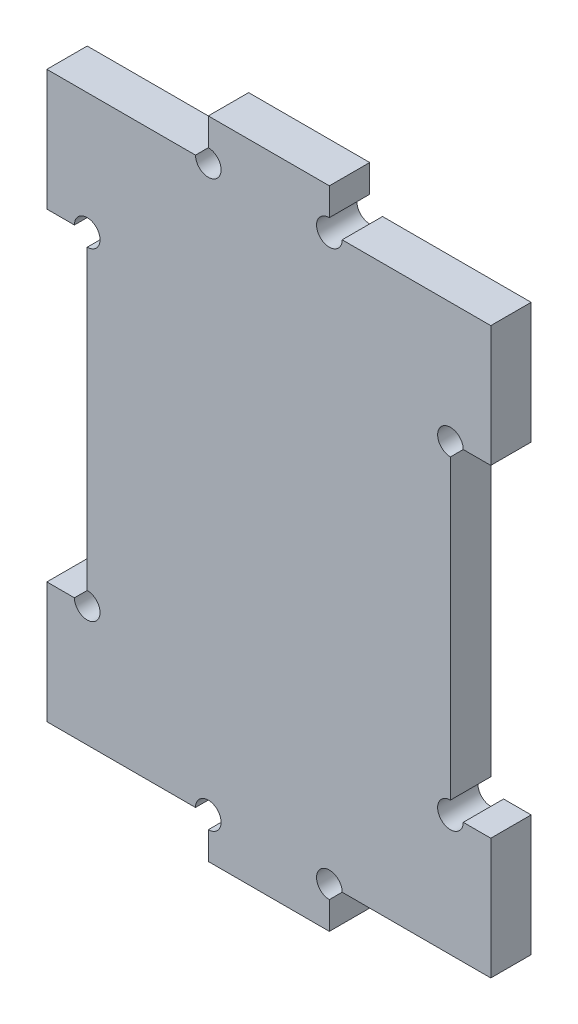
SolidWorks part; units mm, degrees
material "Acrylic (Medium-high impact)"
ref_plane "Front Plane" through (0, 0, 0) normal (0, 0, 1) x (1, 0, 0)
ref_plane "Top Plane" through (0, 0, 0) normal (0, 1, 0) x (1, 0, 0)
ref_plane "Right Plane" through (0, 0, 0) normal (1, 0, 0) x (0, 0, -1)
sketch "Sketch2" plane through (0, 0, 0) normal (0, 0, 1) x (1, 0, 0)
  line L0 (-7.5, 40) -> (7.5, 40)
  line L1 (7.5, 40) -> (7.5, 35)
  line L2 (7.5, 35) -> (27.5, 35)
  line L3 (27.5, 35) -> (27.5, -35)
  line L4 (0, 0) -> (27.5, 0) construction
  line L5 (0, -40) -> (0, 40) construction
  line L6 (-27.5, 35) -> (-27.5, -35)
  line L7 (-7.5, 35) -> (-27.5, 35)
  line L8 (-7.5, 40) -> (-7.5, 35)
  line L9 (-7.5, -40) -> (-7.5, -35)
  line L10 (-7.5, -35) -> (-27.5, -35)
  line L11 (7.5, -35) -> (27.5, -35)
  line L12 (7.5, -40) -> (7.5, -35)
  line L13 (-7.5, -40) -> (7.5, -40)
  point P17 (-27.5, 0)
  dimension "D1" = 5
  dimension "D2" = 27.5
  dimension "D3" = 7.5
  dimension "D4" = 40
extrude "Boss-Extrude2" add sketch "Sketch2" along normal blind 5
sketch "Sketch3" plane through (0, 0, 5) normal (0, 0, 1) x (1, 0, 0)
  line L0 (0, 0) -> (-27.5, 0) construction
  line L1 (-27.5, 35) -> (-27.5, -35) construction
  line L3 (-22.5, -20) -> (-27.5, -20)
  line L4 (-22.5, -20) -> (-22.5, 20)
  line L5 (-22.5, 20) -> (-27.5, 20)
  line L6 (-27.5, -20) -> (-27.5, 20)
  line L7 (-22.5, -20) -> (-27.5, 20) construction
  line L8 (-22.5, 20) -> (-27.5, -20) construction
  point P5 (-25, 0)
  point P8 (-27.5, 0)
  dimension "D1" = 40
  dimension "D2" = 5
extrude "Cut-Extrude1" cut sketch "Sketch3" against normal blind 5
mirror "Mirror1" about plane through (0, 0, 0) normal (1, 0, 0) of "Cut-Extrude1"
sketch "Sketch4" plane through (0, 0, 5) normal (0, 0, 1) x (1, 0, 0)
  circle A0 centre (-22.5, 20) radius 1.5875
  circle A1 centre (-7.5, 35) radius 1.5875
  circle A2 centre (7.5, 35) radius 1.5875
  circle A3 centre (22.5, 20) radius 1.5875
  circle A4 centre (22.5, -20) radius 1.5875
  circle A5 centre (7.5, -35) radius 1.5875
  circle A6 centre (-7.5, -35) radius 1.5875
  circle A7 centre (-22.5, -20) radius 1.5875
  dimension "D1" = 3.175
extrude "Cut-Extrude2" cut sketch "Sketch4" against normal through all
equation "\"cortador\"=4.59045"
